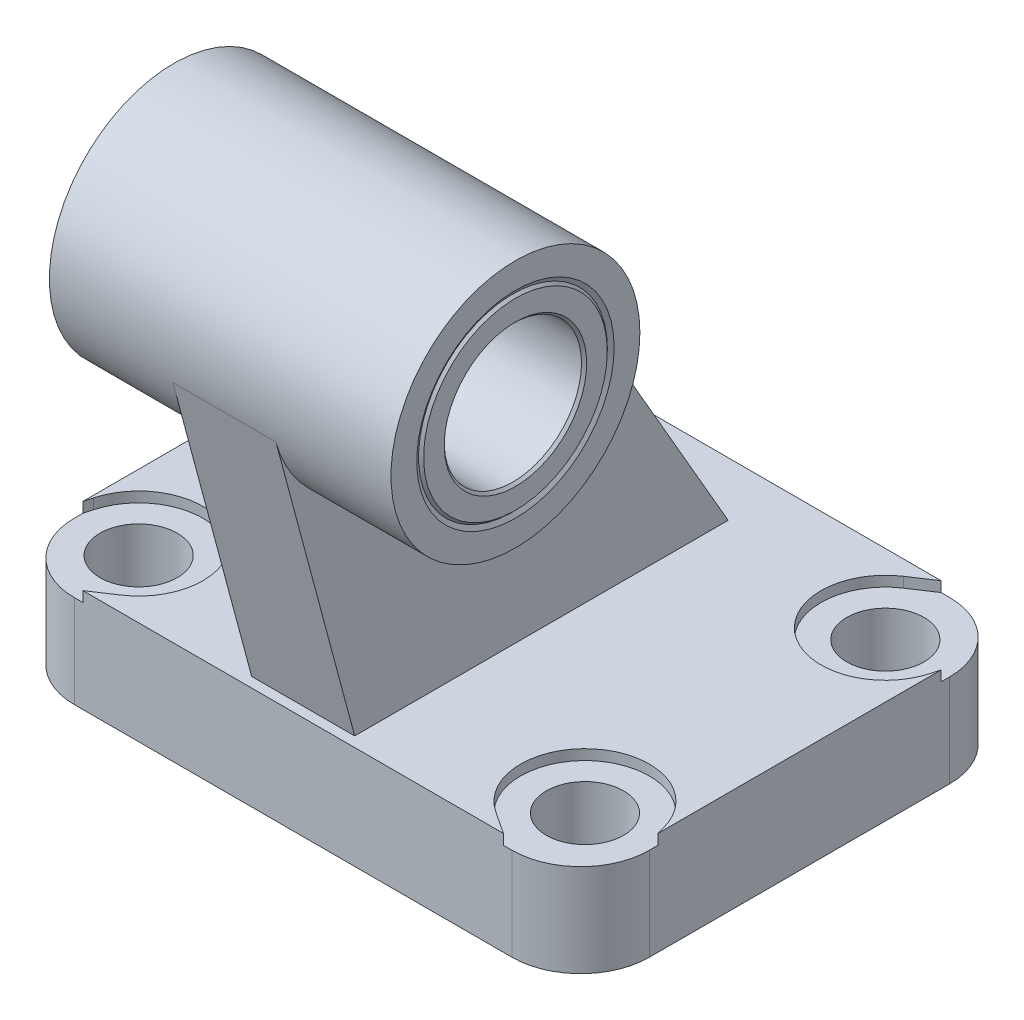
SolidWorks part; units mm, degrees
ref_plane "Front Plane" through (0, 0, 0) normal (0, 0, 1) x (1, 0, 0)
ref_plane "Top Plane" through (0, 0, 0) normal (0, 1, 0) x (1, 0, 0)
ref_plane "Right Plane" through (0, 0, 0) normal (1, 0, 0) x (0, 0, -1)
ref_plane "Plane1" through (0, 0, 0) normal (0, 1, 0) x (1, 0, 0)
sketch "Sketch1" plane through (0, 0, 0) normal (0, 1, 0) x (1, 0, 0)
  line L0 (-25.5, -25.5) -> (25.5, -25.5)
  line L1 (33.5, -17.5) -> (33.5, 17.5)
  line L2 (25.5, 25.5) -> (-25.5, 25.5)
  line L3 (-33.5, 17.5) -> (-33.5, -17.5)
  arc A0 (-33.5, -17.5) -> (-25.5, -25.5) centre (-25.5, -17.5) ccw
  arc A1 (25.5, -25.5) -> (33.5, -17.5) centre (25.5, -17.5) ccw
  arc A2 (33.5, 17.5) -> (25.5, 25.5) centre (25.5, 17.5) ccw
  arc A3 (-25.5, 25.5) -> (-33.5, 17.5) centre (-25.5, 17.5) ccw
extrude "Boss-Extrude1" add sketch "Sketch1" along normal blind 12
ref_plane "Plane2" through (0, 0, 0) normal (1, 0, 0) x (0, 0, -1)
sketch "Sketch2" plane through (0, 0, 0) normal (1, 0, 0) x (0, 0, -1)
  line L0 (-33.5059, 46.2471) -> (-24.3294, 12)
  line L1 (-24.3294, 12) -> (19.1825, 12)
  line L2 (19.1825, 12) -> (-6.9426, 57.25)
  line L3 (-6.9426, 57.25) -> (-33.5059, 46.2471)
extrude "Boss-Extrude2" add sketch "Sketch2" against normal blind 6 and the other way blind 6
ref_plane "Plane3" through (0, 0, 0) normal (1, 0, 0) x (0, 0, -1)
sketch "Sketch3" plane through (0, 0, 0) normal (1, 0, 0) x (0, 0, -1)
  circle A0 centre (-19.5, 50) radius 14.5
extrude "Boss-Extrude3" add sketch "Sketch3" against normal blind 19.9 and the other way blind 19.9
ref_plane "Plane4" through (0, 12, 0) normal (0, 1, 0) x (1, 0, 0)
sketch "Sketch4" plane through (0, 12, 0) normal (0, 1, 0) x (1, 0, 0)
  line L0 (-67, -51) -> (67, -51)
  line L1 (67, -51) -> (67, 51)
  line L2 (67, 51) -> (-67, 51)
  line L3 (-67, 51) -> (-67, -51)
  line L4 (-33.5, 16.5) -> (-33.5, -16.5)
  line L5 (-33.5, -16.5) -> (-33.238, -15.5349)
  line L6 (-21.8625, -23.7555) -> (-24.5, -25.5)
  line L7 (-24.5, -25.5) -> (24.5, -25.5)
  line L8 (24.5, -25.5) -> (21.8625, -23.7555)
  line L9 (33.238, -15.5349) -> (33.5, -16.5)
  line L10 (33.5, -16.5) -> (33.5, 16.5)
  line L11 (33.5, 16.5) -> (33.238, 15.5349)
  line L12 (21.8625, 23.7555) -> (24.5, 25.5)
  line L13 (24.5, 25.5) -> (-24.5, 25.5)
  line L14 (-24.5, 25.5) -> (-21.8625, 23.7555)
  line L15 (-33.238, 15.5349) -> (-33.5, 16.5)
  arc A0 (-33.238, -15.5349) -> (-21.8625, -23.7555) centre (-26, -17.5) cw
  arc A1 (21.8625, -23.7555) -> (33.238, -15.5349) centre (26, -17.5) cw
  arc A2 (33.238, 15.5349) -> (21.8625, 23.7555) centre (26, 17.5) cw
  arc A3 (-21.8625, 23.7555) -> (-33.238, 15.5349) centre (-26, 17.5) cw
extrude "Cut-Extrude1" cut sketch "Sketch4" against normal blind 1.2
ref_plane "Plane5" through (0, 0, 17.5) normal (0, 0, 1) x (1, 0, 0)
sketch "Sketch5" plane through (0, 0, 17.5) normal (0, 0, 1) x (1, 0, 0)
  line L0 (-26, 0) -> (-30.5, 0)
  line L1 (-30.5, 0) -> (-30.5, 10.8)
  line L2 (-30.5, 10.8) -> (-33.5, 10.8)
  line L3 (-33.5, 10.8) -> (-33.5, 12)
  line L4 (-33.5, 12) -> (-26, 12)
  line L5 (-26, 12) -> (-26, 0)
  line L6 (-26, 12) -> (-26, 0) construction
revolve "Cut-Revolve1" cut sketch "Sketch5" angle 360 about L6
ref_plane "Plane6" through (0, 0, -17.5) normal (0, 0, 1) x (1, 0, 0)
sketch "Sketch6" plane through (0, 0, -17.5) normal (0, 0, 1) x (1, 0, 0)
  line L0 (-26, 0) -> (-30.5, 0)
  line L1 (-30.5, 0) -> (-30.5, 10.8)
  line L2 (-30.5, 10.8) -> (-33.5, 10.8)
  line L3 (-33.5, 10.8) -> (-33.5, 12)
  line L4 (-33.5, 12) -> (-26, 12)
  line L5 (-26, 12) -> (-26, 0)
  line L6 (-26, 12) -> (-26, 0) construction
revolve "Cut-Revolve2" cut sketch "Sketch6" angle 360 about L6
ref_plane "Plane7" through (0, 0, 17.5) normal (0, 0, 1) x (1, 0, 0)
sketch "Sketch7" plane through (0, 0, 17.5) normal (0, 0, 1) x (1, 0, 0)
  line L0 (26, 0) -> (21.5, 0)
  line L1 (21.5, 0) -> (21.5, 10.8)
  line L2 (21.5, 10.8) -> (18.5, 10.8)
  line L3 (18.5, 10.8) -> (18.5, 12)
  line L4 (18.5, 12) -> (26, 12)
  line L5 (26, 12) -> (26, 0)
  line L6 (26, 12) -> (26, 0) construction
revolve "Cut-Revolve3" cut sketch "Sketch7" angle 360 about L6
ref_plane "Plane8" through (0, 0, -17.5) normal (0, 0, 1) x (1, 0, 0)
sketch "Sketch8" plane through (0, 0, -17.5) normal (0, 0, 1) x (1, 0, 0)
  line L0 (26, 0) -> (21.5, 0)
  line L1 (21.5, 0) -> (21.5, 10.8)
  line L2 (21.5, 10.8) -> (18.5, 10.8)
  line L3 (18.5, 10.8) -> (18.5, 12)
  line L4 (18.5, 12) -> (26, 12)
  line L5 (26, 12) -> (26, 0)
  line L6 (26, 12) -> (26, 0) construction
revolve "Cut-Revolve4" cut sketch "Sketch8" angle 360 about L6
ref_plane "Plane9" through (0, 0, 19.5) normal (0, 0, 1) x (1, 0, 0)
sketch "Sketch9" plane through (0, 0, 19.5) normal (0, 0, 1) x (1, 0, 0)
  line L0 (-19.9, 50) -> (-19.9, 61.5)
  line L1 (-19.9, 61.5) -> (-19.6113, 61)
  line L2 (-19.6113, 61) -> (19.6113, 61)
  line L3 (19.6113, 61) -> (19.9, 61.5)
  line L4 (19.9, 61.5) -> (19.9, 50)
  line L5 (19.9, 50) -> (-19.9, 50)
  line L6 (19.9, 50) -> (-19.9, 50) construction
revolve "Cut-Revolve5" cut sketch "Sketch9" angle 360 about L6
ref_plane "Plane10" through (0, 0, 19.5) normal (0, 0, 1) x (1, 0, 0)
sketch "Sketch10" plane through (0, 0, 19.5) normal (0, 0, 1) x (1, 0, 0)
  line L0 (-19.9, 58.3) -> (-19.6, 58)
  line L1 (-19.6, 58) -> (19.6, 58)
  line L2 (19.6, 58) -> (19.9, 58.3)
  line L3 (19.9, 58.3) -> (19.9, 60.7)
  line L4 (19.9, 60.7) -> (19.6, 61)
  line L5 (19.6, 61) -> (-19.6, 61)
  line L6 (-19.6, 61) -> (-19.9, 60.7)
  line L7 (-19.9, 60.7) -> (-19.9, 58.3)
  line L8 (19.9, 50) -> (-19.9, 50) construction
revolve "Revolve1" add sketch "Sketch10" angle 360 about L8
